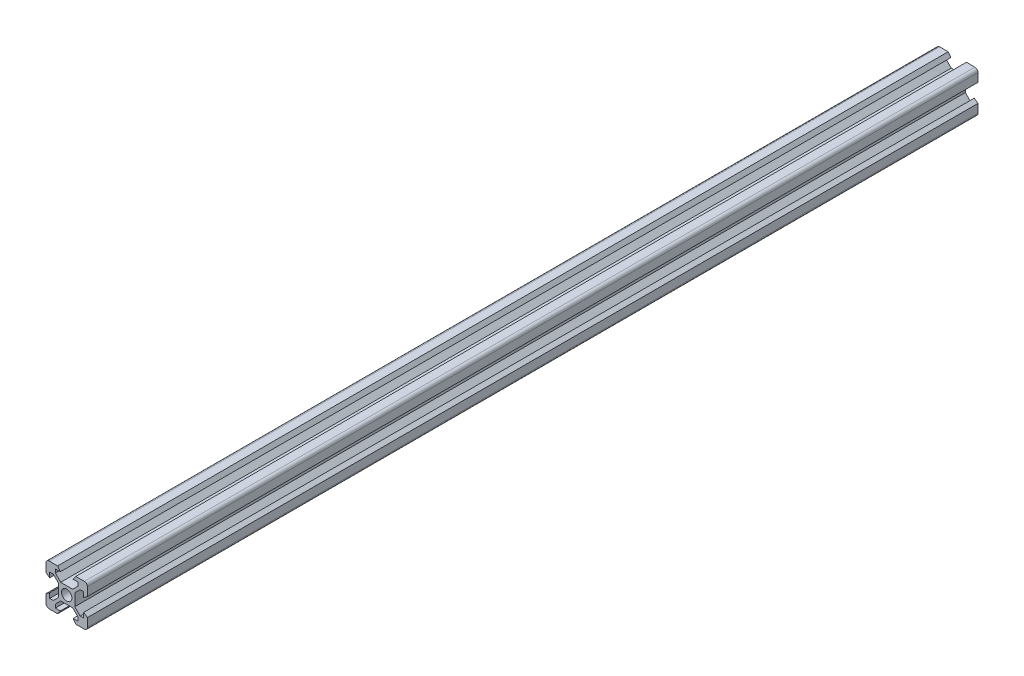
SolidWorks part; units mm, degrees
ref_plane "前视基准面" through (0, 0, 0) normal (0, 0, 1) x (1, 0, 0)
ref_plane "上视基准面" through (0, 0, 0) normal (0, 1, 0) x (1, 0, 0)
ref_plane "右视基准面" through (0, 0, 0) normal (1, 0, 0) x (0, 0, -1)
sketch "草图1" plane through (0, 0, 0) normal (0, 0, 1) x (1, 0, 0)
  line L0 (16.8101, 19.3214) -> (19.4, 21.9114) construction
  line L1 (14.8, 34.8214) -> (18.9, 34.8214)
  line L2 (13.3, 33.3214) -> (13.3, 29.2214)
  line L3 (14.8, 14.8214) -> (18.9, 14.8214)
  line L4 (33.3, 33.3214) -> (33.3, 29.2214)
  line L7 (27.2, 27.7315) -> (29.7899, 30.3214) construction
  line L8 (33.3, 29.2214) -> (31.5, 27.9214)
  line L9 (28.8, 31.3114) -> (26.2101, 28.7214)
  line L10 (31.5, 30.3214) -> (31.5, 27.9214)
  line L11 (29.7899, 30.3214) -> (31.5, 30.3214)
  line L12 (26.2101, 28.7214) -> (28.8, 31.3114) construction
  line L13 (27.2, 27.7315) -> (29.7899, 30.3214)
  line L15 (20.3899, 28.7214) -> (26.2101, 28.7214) construction
  line L18 (18.9, 34.8214) -> (20.2, 33.0214)
  line L19 (27.7, 34.8214) -> (26.4, 33.0214)
  line L20 (26.4, 33.0214) -> (28.8, 33.0214)
  line L21 (28.8, 33.0214) -> (28.8, 31.3114)
  line L22 (26.2101, 28.7214) -> (20.3899, 28.7214)
  line L25 (20.3899, 28.7214) -> (17.8, 31.3114)
  line L26 (17.8, 31.3114) -> (17.8, 33.0214)
  line L27 (17.8, 33.0214) -> (20.2, 33.0214)
  line L28 (27.2, 21.9114) -> (27.2, 27.7315)
  line L29 (29.7899, 19.3214) -> (27.2, 21.9114)
  line L30 (31.5, 19.3214) -> (29.7899, 19.3214)
  line L31 (31.5, 21.7214) -> (31.5, 19.3214)
  line L32 (33.3, 20.4214) -> (31.5, 21.7214)
  line L33 (27.7, 14.8214) -> (26.4, 16.6214)
  line L34 (28.8, 16.6214) -> (26.4, 16.6214)
  line L35 (28.8, 18.3315) -> (28.8, 16.6214)
  line L36 (26.2101, 20.9214) -> (28.8, 18.3315)
  line L37 (20.3899, 20.9214) -> (26.2101, 20.9214)
  line L38 (17.8, 18.3315) -> (20.3899, 20.9214)
  line L39 (17.8, 16.6214) -> (17.8, 18.3315)
  line L40 (20.2, 16.6214) -> (17.8, 16.6214)
  line L41 (18.9, 14.8214) -> (20.2, 16.6214)
  line L42 (13.3, 20.4214) -> (15.1, 21.7214)
  line L43 (15.1, 19.3214) -> (15.1, 21.7214)
  line L44 (16.8101, 19.3214) -> (15.1, 19.3214)
  line L45 (19.4, 21.9114) -> (16.8101, 19.3214)
  line L46 (19.4, 27.7315) -> (19.4, 21.9114)
  line L47 (16.8101, 30.3214) -> (19.4, 27.7315)
  line L48 (15.1, 30.3214) -> (16.8101, 30.3214)
  line L49 (15.1, 27.9214) -> (15.1, 30.3214)
  line L50 (13.3, 29.2214) -> (15.1, 27.9214)
  line L51 (27.7, 34.8214) -> (31.8, 34.8214)
  line L52 (33.3, 20.4214) -> (33.3, 16.3214)
  line L53 (13.3, 20.4214) -> (13.3, 16.3214)
  line L54 (27.7, 14.8214) -> (31.8, 14.8214)
  circle A0 centre (23.3, 24.8214) radius 2.5
  arc A1 (14.8, 34.8214) -> (13.3, 33.3214) centre (14.8, 33.3214) ccw
  arc A2 (33.3, 33.3214) -> (31.8, 34.8214) centre (31.8, 33.3214) ccw
  arc A3 (31.8, 14.8214) -> (33.3, 16.3214) centre (31.8, 16.3214) ccw
  arc A4 (14.8, 14.8214) -> (13.3, 16.3214) centre (14.8, 16.3214) cw
  point P11 (33.3, 34.8214)
  point P18 (33.3, 14.8214)
  dimension "D3" = 5
  dimension "D1" = 1.5
  dimension "D4" = 1.5
  dimension "D5" = 1.5
  dimension "D7" = 1.5
  dimension "D2" = 20
  dimension "D6" = 4
extrude "凸台-拉伸1" add sketch "草图1" along normal blind 430
